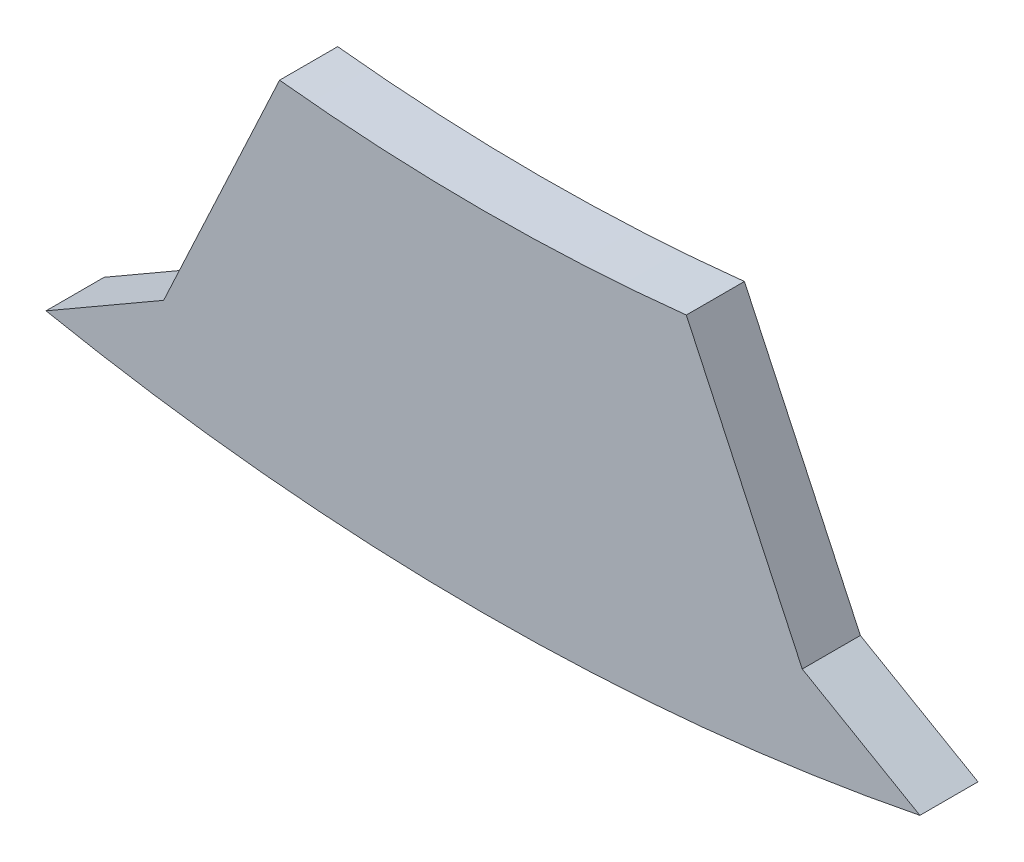
SolidWorks part; units mm, degrees
ref_plane "Front Plane" through (0, 0, 0) normal (0, 0, 1) x (1, 0, 0)
ref_plane "Top Plane" through (0, 0, 0) normal (0, 1, 0) x (1, 0, 0)
ref_plane "Right Plane" through (0, 0, 0) normal (1, 0, 0) x (0, 0, -1)
sketch "Sketch1" plane through (0, 0, 0) normal (0, 0, 1) x (1, 0, 0)
  line L0 (0, 0) -> (0, -19.6734) construction
  line L1 (-5.4952, -36.5897) -> (-3.5, -32.311)
  line L2 (-5.4952, -36.5897) -> (-7.5197, -37.7585)
  line L3 (5.4952, -36.5897) -> (7.5197, -37.7585)
  line L4 (5.4952, -36.5897) -> (3.5, -32.311)
  line L5 (-5.2724, -35.1063) -> (-5.718, -38.073) construction
  arc A0 (-3.5, -32.311) -> (3.5, -32.311) centre (0, 0) ccw
  arc A1 (-7.5197, -37.7585) -> (7.5197, -37.7585) centre (0, 0) ccw
  arc A2 (-5.2724, -35.1063) -> (4.8329, -35.1695) centre (0, 0) ccw construction
  arc A3 (-3.9457, -33.2668) -> (3.9457, -33.2668) centre (0, 0) ccw construction
  point P1 (-5.4952, -36.5897)
  point P15 (-5.4952, -36.5897)
  point P16 (-3.9457, -33.2668)
  point P17 (3.9457, -33.2668)
  point P18 (-10.9041, -31.6757)
  dimension "D1" = 5
  dimension "D2" = 3
  dimension "D3" = 77
  dimension "D4" = 1
  dimension "D5" = 7
  dimension "D6" = 25
  dimension "D7" = 60
extrude "Boss-Extrude1" add sketch "Sketch1" along normal blind 1
scale "Scale1" scale about centroid uniform scaling yes scale factor 0.97
